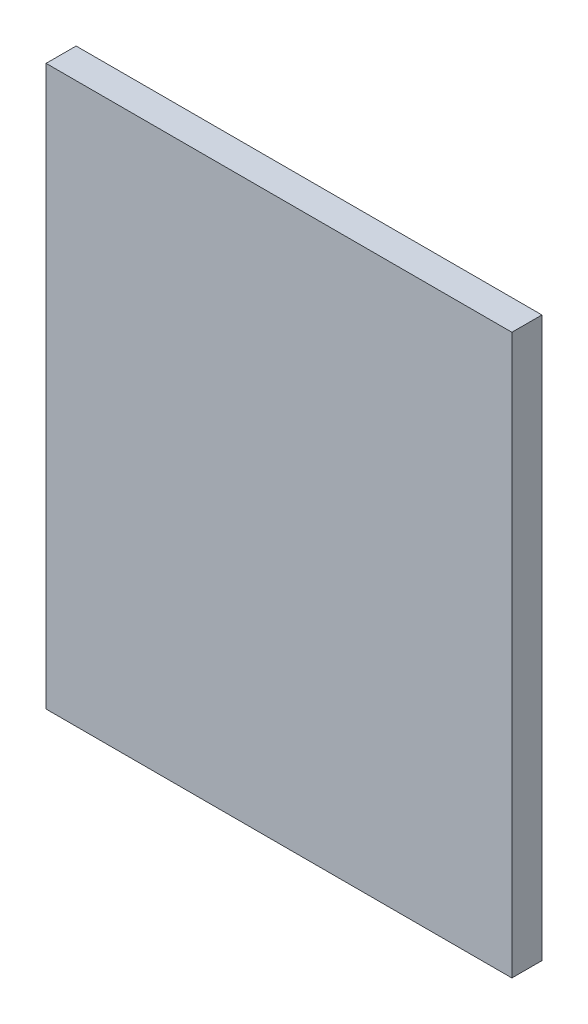
SolidWorks part; units mm, degrees
material "Ceramic Porcelain2"
ref_plane "Front Plane" through (0, 0, 0) normal (0, 0, 1) x (1, 0, 0)
ref_plane "Top Plane" through (0, 0, 0) normal (0, 1, 0) x (1, 0, 0)
ref_plane "Right Plane" through (0, 0, 0) normal (1, 0, 0) x (0, 0, -1)
ref_plane "Plane1" through (0, 0, 0) normal (0, 0, -1) x (-1, 0, 0)
sketch "Sketch1" plane through (0, 0, 0) normal (0, 0, -1) x (-1, 0, 0)
  line L0 (-6.98, 8.38) -> (-6.98, 0)
  line L1 (-6.98, 0) -> (0, 0)
  line L2 (0, 0) -> (0, 8.38)
  line L3 (0, 8.38) -> (-6.98, 8.38)
extrude "Boss-Extrude1" add sketch "Sketch1" against normal blind 0.45
